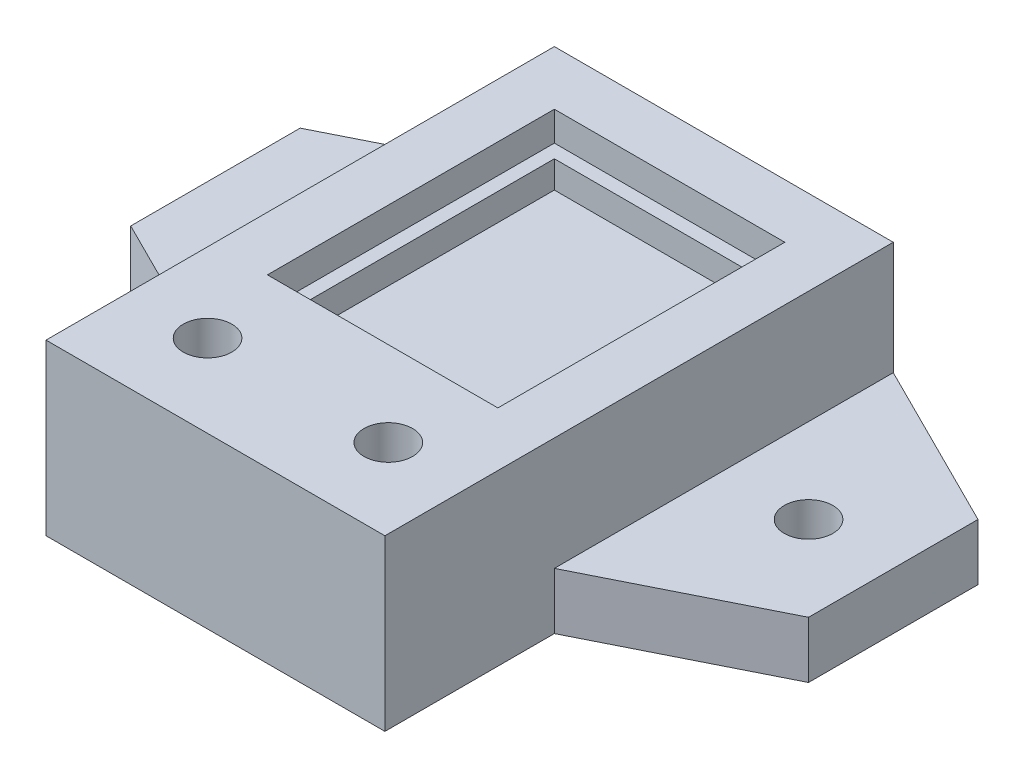
SolidWorks part; units mm, degrees
ref_plane "Front Plane" through (0, 0, 0) normal (0, 0, 1) x (1, 0, 0)
ref_plane "Top Plane" through (0, 0, 0) normal (0, 1, 0) x (1, 0, 0)
ref_plane "Right Plane" through (0, 0, 0) normal (1, 0, 0) x (0, 0, -1)
sketch "Sketch1" plane through (0, 0, 0) normal (0, 1, 0) x (1, 0, 0)
  line L0 (0, 0) -> (0, 15)
  line L1 (0, 15) -> (15, 22.5)
  line L2 (15, 22.5) -> (45, 22.5)
  line L3 (45, 22.5) -> (60, 15)
  line L4 (60, 15) -> (60, 0)
  line L5 (60, 0) -> (45, -7.5)
  line L6 (45, -7.5) -> (15, -7.5)
  line L7 (15, -7.5) -> (0, 0)
  line L8 (15, 22.5) -> (15, -7.5)
  line L9 (45, -7.5) -> (45, 22.5)
  point P3 (30, 22.5)
  point P10 (30, -7.5)
  point P11 (7.5, 7.5)
  point P12 (52.5, 7.5)
  point P17 (60, 7.5)
  point P18 (7.5, 18.75)
  point P19 (52.5, 18.75)
  dimension "D1" = 30
  dimension "D2" = 15
  dimension "D3" = 30
  dimension "D4" = 15
extrude "Boss-Extrude1" add sketch "Sketch1" along normal blind 5 contours L8 L1 L0 L7 | L6 L9 L2 L8 | L9 L5 L4 L3
hole_wizard "M4 Clearance Hole1" positions "Sketch4" profile "Sketch5" hole size "M4" standard "ISO" end condition up to next
sketch "Sketch4" plane through (0, 0, 0) normal (0, -1, 0) x (-1, 0, 0)
  point P0 (-7.5, 7.5)
  point P3 (-52.5, 7.5)
sketch "Sketch5" plane through (7.5, 0, -7.5) normal (1, 0, 0) x (0, 0, -1)
  line L0 (0, 0) -> (0, 5)
  line L1 (0, 5) -> (2.15, 5)
  line L2 (2.15, 5) -> (2.15, 0)
  line L5 (2.15, 0) -> (0, 0)
  line L11 (0, -6.35) -> (0, 107.95) construction
  dimension "Thru Hole Dia." = 4.3
  dimension "Thru Hole Depth" = 5
sketch "Sketch13" plane through (0, 0, 0) normal (0, 1, 0) x (1, 0, 0)
  line L0 (45, -7.5) -> (15, -7.5) construction
  line L1 (15, 22.5) -> (45, 22.5)
  line L2 (15, 22.5) -> (15, -22.5)
  line L3 (15, -22.5) -> (45, -22.5)
  line L4 (45, 22.5) -> (45, -22.5)
  dimension "D1" = 15
extrude "Boss-Extrude7" add sketch "Sketch13" along normal blind 15
sketch "Sketch14" plane through (0, 15, 0) normal (0, 1, 0) x (1, 0, 0)
  line L1 (19.8, -7.7) -> (40.2, -7.7)
  line L2 (19.8, -7.7) -> (19.8, 17.7)
  line L3 (19.8, 17.7) -> (40.2, 17.7)
  line L4 (40.2, -7.7) -> (40.2, 17.7)
  line L5 (19.8, -7.7) -> (40.2, 17.7) construction
  line L6 (19.8, 17.7) -> (40.2, -7.7) construction
  line L7 (45, 22.5) -> (15, 22.5) construction
  line L8 (19.8, 17.7) -> (19.8, 22.5) construction
  line L9 (19.8, 17.7) -> (15, 17.7) construction
  line L10 (15, 22.5) -> (15, -22.5) construction
  point P0 (30, 5)
  point P10 (30, 22.5)
  dimension "D1" = 20.4
  dimension "D2" = 25.4
extrude "Cut-Extrude2" cut sketch "Sketch14" against normal blind 5
sketch "Sketch15" plane through (0, 15, 0) normal (0, 1, 0) x (1, 0, 0)
  line L0 (19.8, -7.7) -> (40.2, -7.7) construction
  line L1 (40.2, -7.7) -> (40.2, 17.7) construction
  line L2 (40.2, 17.7) -> (19.8, 17.7) construction
  line L3 (19.8, 17.7) -> (19.8, -7.7) construction
  line L4 (19.8, -7.7) -> (40.2, -7.7) construction
  line L5 (40.2, -7.7) -> (40.2, 17.7) construction
  line L6 (40.2, 17.7) -> (19.8, 17.7) construction
  line L7 (19.8, 17.7) -> (19.8, -7.7) construction
  line L8 (21, 16.5) -> (21, -6.5)
  line L9 (21, -6.5) -> (39, -6.5)
  line L10 (39, -6.5) -> (39, 16.5)
  line L11 (39, 16.5) -> (21, 16.5)
  line M9 (40.2, 17.7) -> (40.2, -7.7)
  line M10 (40.2, -7.7) -> (19.8, -7.7)
  line M11 (19.8, -7.7) -> (19.8, 17.7)
  line M12 (19.8, 17.7) -> (40.2, 17.7)
  dimension "D1" = 1.2
extrude "Boss-Extrude8" add sketch "Sketch15" against normal up to next from offset 2.6 contours L11 L10 L9 L8 M9 M12 M11 M10 offset against normal yes
hole_wizard "M4 Clearance Hole2" positions "Sketch9" profile "Sketch10" hole size "M4" standard "ISO" end condition up to next
sketch "Sketch9" plane through (0, 15, 0) normal (0, 1, 0) x (1, 0, 0)
  line L0 (22, -15.2) -> (38, -15.2) construction
  line L2 (45, -7.5) -> (15, -7.5) construction
  line L5 (45, 22.5) -> (15, 22.5) construction
  line L6 (19.8, -7.7) -> (40.2, -7.7) construction
  point P0 (22, -15.2)
  point P2 (38, -15.2)
  point P10 (30, -15.2)
  point P13 (30, -7.5)
  point P21 (30, 22.5)
  dimension "D1" = 16
  dimension "D2" = 7.5
sketch "Sketch10" plane through (22, 15, 15.2) normal (1, 0, 0) x (0, 0, 1)
  line L0 (0, 0) -> (0, 15)
  line L1 (0, 15) -> (2.15, 15)
  line L2 (2.15, 15) -> (2.15, 0)
  line L5 (2.15, 0) -> (0, 0)
  line L11 (0, -6.35) -> (0, 107.95) construction
  dimension "Thru Hole Dia." = 4.3
  dimension "Thru Hole Depth" = 15
sketch "Sketch11" plane through (0, 0, 0) normal (0, 1, 0) x (-1, 0, 0)
  line L1 (-22, 19.2415) -> (-25.5, 17.2207)
  line L2 (-25.5, 17.2207) -> (-25.5, 13.1793)
  line L3 (-25.5, 13.1793) -> (-22, 11.1585)
  line L4 (-22, 11.1585) -> (-18.5, 13.1793)
  line L5 (-18.5, 13.1793) -> (-18.5, 17.2207)
  line L6 (-18.5, 17.2207) -> (-22, 19.2415)
  circle A0 centre (-22, 15.2) radius 3.5 construction
  dimension "D1" = 7
extrude "Cut-Extrude1" cut sketch "Sketch11" along normal blind 5
ref_plane "Plane1" through (30, 0, 0) normal (1, 0, 0) x (0, 0, -1)
mirror "Mirror1" about plane through (30, 0, 0) normal (1, 0, 0) of "Cut-Extrude1"
